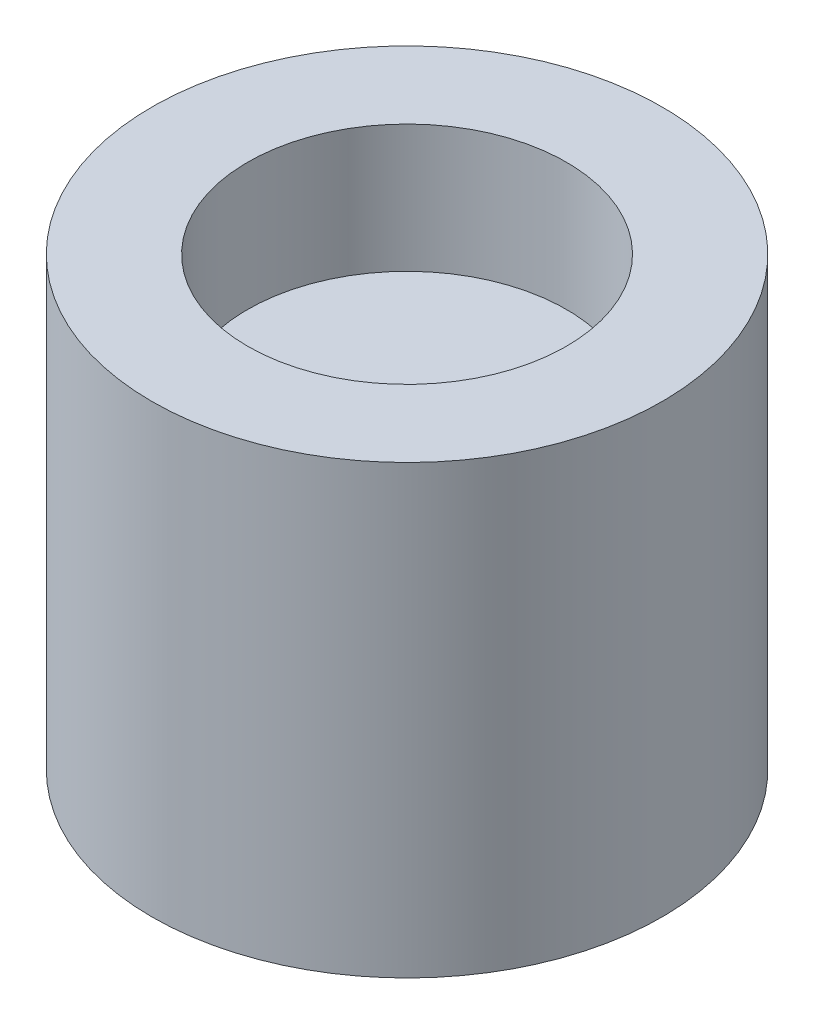
SolidWorks part; units mm, degrees
ref_plane "Front Plane" through (0, 0, 0) normal (0, 0, 1) x (1, 0, 0)
ref_plane "Top Plane" through (0, 0, 0) normal (0, 1, 0) x (1, 0, 0)
ref_plane "Right Plane" through (0, 0, 0) normal (1, 0, 0) x (0, 0, -1)
sketch "Sketch1" plane through (0, 0, 0) normal (0, 1, 0) x (1, 0, 0)
  circle A0 centre (0, 0) radius 5.08
  dimension "D1" = 10.16
extrude "Boss-Extrude1" add sketch "Sketch1" along normal blind 8.89
sketch "Sketch2" plane through (0, 0, 0) normal (0, 1, 0) x (1, 0, 0)
  line L0 (-2.794, -1.9879) -> (-2.794, 1.9879)
  line L1 (0, 0) -> (-2.794, 0) construction
  circle A0 centre (0, 0) radius 3.429
  dimension "D1" = 6.858
  dimension "D2" = 2.794
extrude "Cut-Extrude1" cut sketch "Sketch2" along normal blind 3.81
sketch "Sketch3" plane through (0, 8.89, 0) normal (0, 1, 0) x (1, 0, 0)
  circle A0 centre (0, 0) radius 3.175
  dimension "D1" = 6.35
extrude "Cut-Extrude2" cut sketch "Sketch3" against normal blind 2.54
